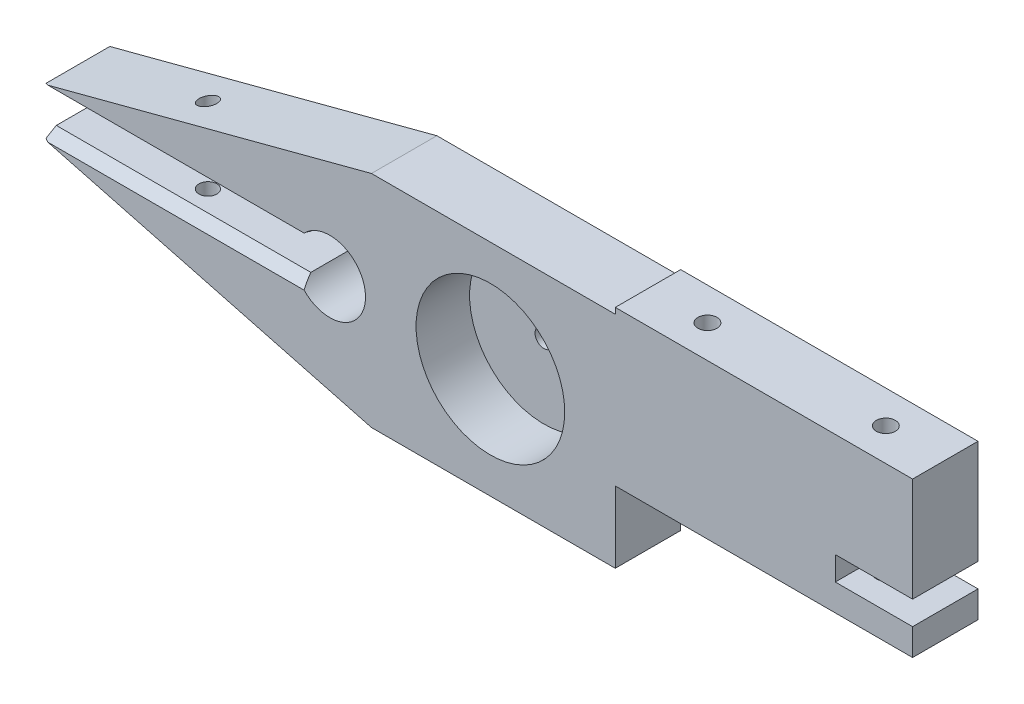
SolidWorks part; units mm, degrees
material "Pine"
ref_plane "Front Plane" through (0, 0, 0) normal (0, 0, 1) x (1, 0, 0)
ref_plane "Top Plane" through (0, 0, 0) normal (0, 1, 0) x (1, 0, 0)
ref_plane "Right Plane" through (0, 0, 0) normal (1, 0, 0) x (0, 0, -1)
sketch "Sketch1" plane through (0, 0, 0) normal (0, 0, 1) x (1, 0, 0)
  line L0 (61, -2) -> (61, -6.5)
  line L1 (61, 19.5) -> (11, 19.5)
  line L2 (61, 19.5) -> (61, 2)
  line L3 (61, -6.5) -> (11, -6.5)
  line L4 (-30, 18.5) -> (-85, 4)
  line L5 (-30, 18.5) -> (11, 18.5)
  line L7 (11, -6.5) -> (11, -18.5)
  line L8 (-85, -4) -> (-85, -3)
  line L9 (61, 2) -> (48, 2)
  line L10 (11, -18.5) -> (-30, -18.5)
  line L11 (61, -2) -> (48, -2)
  line L12 (48, 2) -> (48, -2)
  line L13 (-85, -3) -> (-42.1962, -3)
  line L14 (-85, 4) -> (-85, 3)
  line L15 (-85, -4) -> (-30, -18.5)
  line L16 (-85, 3) -> (-42.1962, 3)
  line L17 (0, 18.5) -> (0, -18.5) construction
  line L18 (0, 0) -> (-37, 0) construction
  line L19 (-85, 3) -> (-85, -3) construction
  line L20 (-85, 0) -> (-37, 0) construction
  line L21 (0, 0) -> (48, 0) construction
  line L22 (11, 19.5) -> (11, 18.5)
  arc A0 (-42.1962, -3) -> (-42.1962, 3) centre (-37, 0) ccw
  dimension "D8" = 6
  dimension "D2" = 1
  dimension "D3" = 26
  dimension "D4" = 4
  dimension "D5" = 13
  dimension "D6" = 1
  dimension "D7" = 6
  dimension "D9" = 30
  dimension "D10" = 11
  dimension "D11" = 55
  dimension "D12" = 37
  dimension "D13" = 37
  dimension "D14" = 61
extrude "Extrude1" add sketch "Sketch1" along normal mid plane 11
sketch "Sketch2" plane through (0, 0, 0) normal (0, 1, 0) x (1, 0, 0)
  line L0 (0, 0) -> (21, 0) construction
  line L1 (21, 0) -> (51, 0) construction
  line L2 (0, 0) -> (-63, 0) construction
  line L3 (61, -5.5) -> (61, 5.5) construction
  circle A0 centre (21, 0) radius 1.6
  circle A1 centre (51, 0) radius 1.6
  circle A2 centre (-63, 0) radius 1.5
  dimension "D1" = 3.2
  dimension "D4" = 3
  dimension "D2" = 30
  dimension "D3" = 10
  dimension "D5" = 63
extrude "Cut-Extrude1" cut sketch "Sketch2" against normal through all and the other way through all
chamfer "Chamfer1" distance 2 angle 30 2 edges at (-63.5981, -3, 5.5) (-63.5981, 3, 5.5)
sketch "Sketch3" plane through (0, 0, 0) normal (0, 1, 0) x (1, 0, 0)
  line L0 (-10, 5.5) -> (-10, 16.5) construction
  line L1 (-10, 5.5) -> (-8.5, 5.5)
  line L2 (-10, 5.5) -> (-10, -5.5)
  line L3 (-10, -5.5) -> (2.5, -5.5)
  line L4 (2.5, 3.5) -> (2.5, -5.5)
  line L5 (11, 5.5) -> (-30, 5.5) construction
  line L6 (11, -5.5) -> (-30, -5.5) construction
  line L7 (2.5, 3.5) -> (-8.5, 3.5)
  line L8 (-8.5, 5.5) -> (-8.5, 3.5)
  dimension "D1" = 2
  dimension "D2" = 3
  dimension "D3" = 25
  dimension "D4" = 10
revolve "Cut-Revolve1" cut sketch "Sketch3" angle 360 about L0
